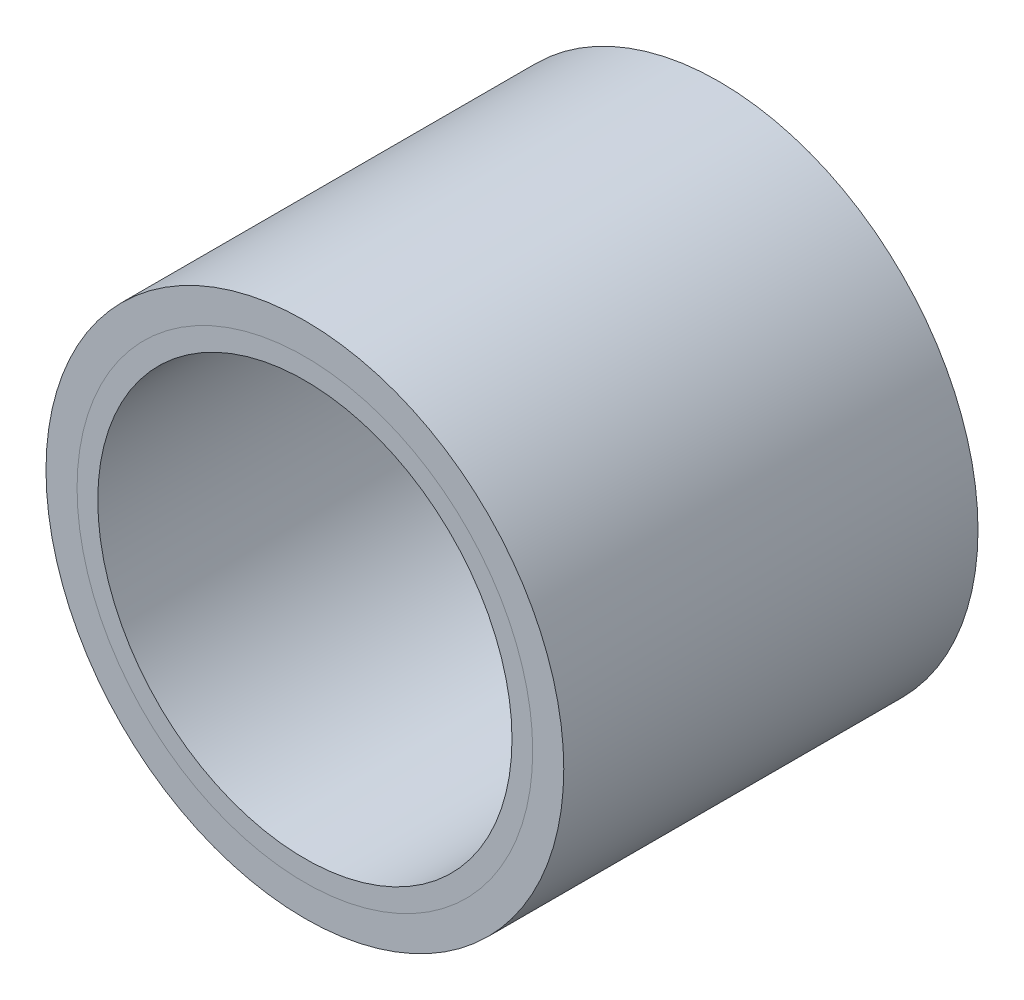
SolidWorks part; units mm, degrees
ref_plane "Front Plane" through (0, 0, 0) normal (0, 0, 1) x (1, 0, 0)
ref_plane "Top Plane" through (0, 0, 0) normal (0, 1, 0) x (1, 0, 0)
ref_plane "Right Plane" through (0, 0, 0) normal (1, 0, 0) x (0, 0, -1)
sketch "Sketch2" plane through (0, 0, 0) normal (0, 0, 1) x (1, 0, 0)
  circle A0 centre (0, 0) radius 10
  circle A1 centre (0, 0) radius 11
  dimension "D1" = 20
  dimension "D2" = 22
extrude "Boss-Extrude1" add sketch "Sketch2" along normal mid plane 20
sketch "Sketch3" plane through (0, 0, 10) normal (0, 0, 1) x (1, 0, 0)
  circle A0 centre (0, 0) radius 12.5
  circle A1 centre (0, 0) radius 11 construction
  circle A2 centre (0, 0) radius 11
  dimension "D1" = 25
extrude "Boss-Extrude2" add sketch "Sketch3" against normal through all separate body
